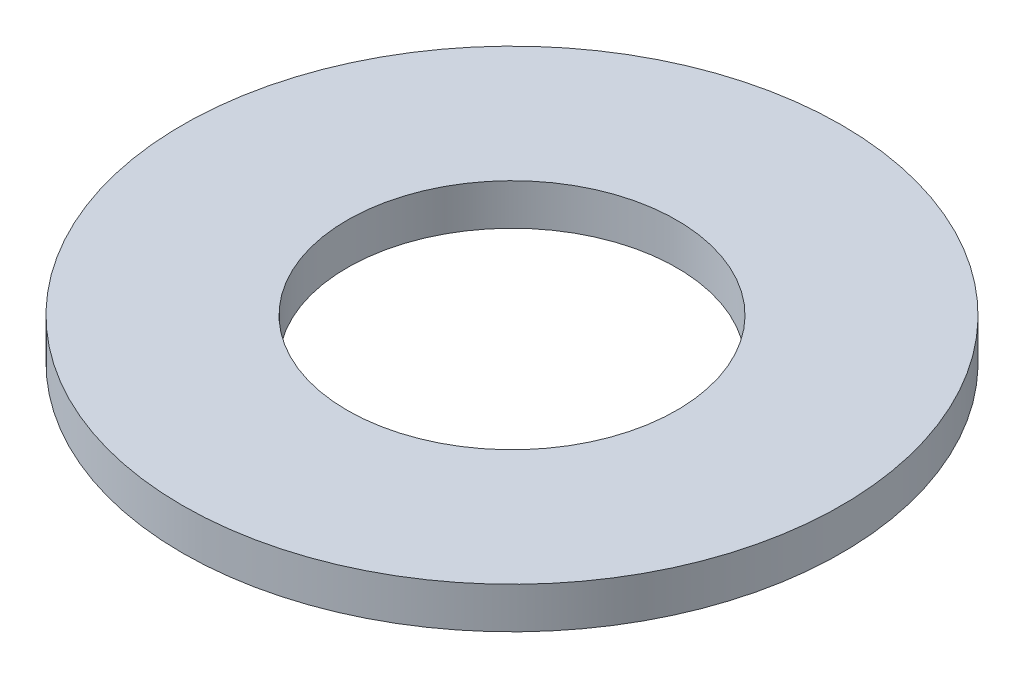
SolidWorks part; units mm, degrees
ref_plane "Front Plane" through (0, 0, 0) normal (0, 0, 1) x (1, 0, 0)
ref_plane "Top Plane" through (0, 0, 0) normal (0, 1, 0) x (1, 0, 0)
ref_plane "Right Plane" through (0, 0, 0) normal (1, 0, 0) x (0, 0, -1)
sketch "Sketch1" plane through (0, 0, 0) normal (0, 1, 0) x (1, 0, 0)
  circle A0 centre (0, 0) radius 8
  circle A1 centre (0, 0) radius 4
extrude "Extrude1" add sketch "Sketch1" along normal blind 1
